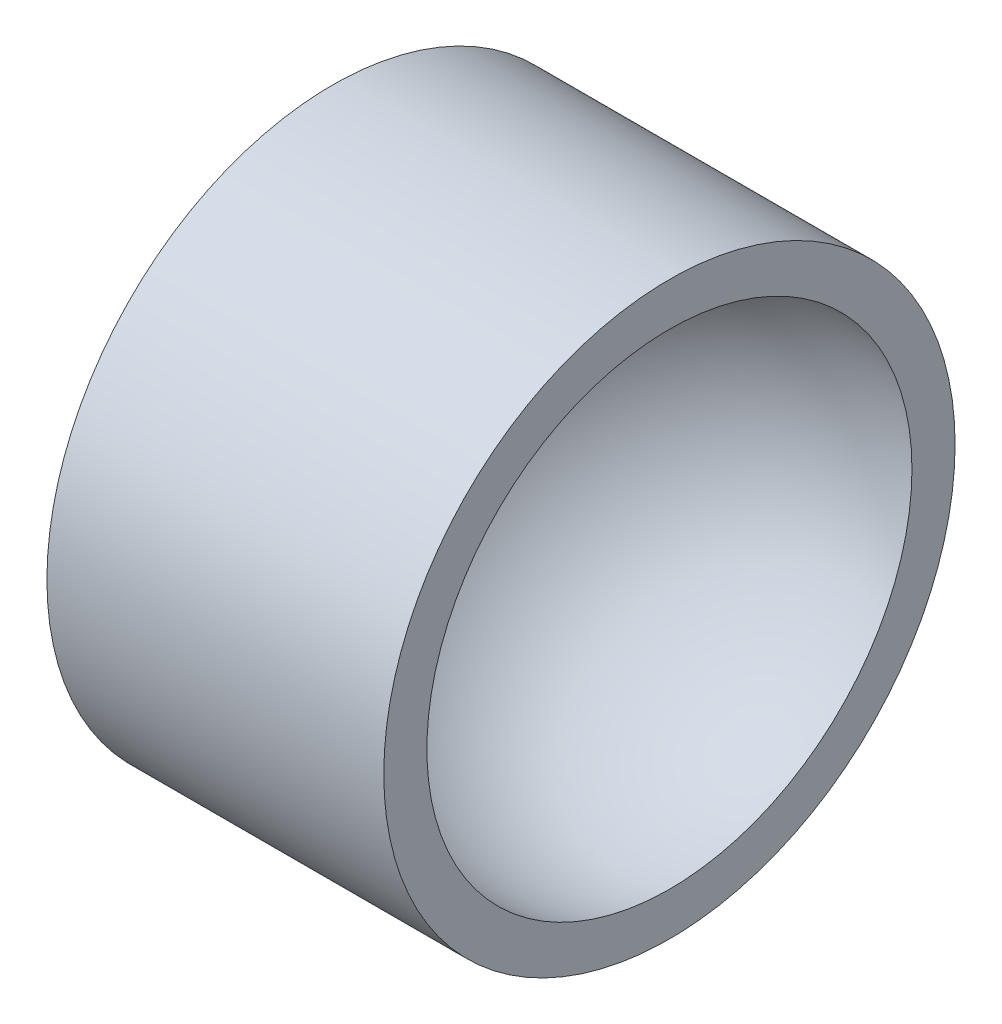
SolidWorks part; units mm, degrees
ref_plane "Alzado" through (0, 0, 0) normal (0, 0, 1) x (1, 0, 0)
ref_plane "Planta" through (0, 0, 0) normal (0, 1, 0) x (1, 0, 0)
ref_plane "Vista lateral" through (0, 0, 0) normal (1, 0, 0) x (0, 0, -1)
sketch "Croquis1" plane through (0, 0, 0) normal (0, 1, 0) x (1, 0, 0)
  line L0 (-10, 0) -> (-12.141, 0)
  line L1 (1.5747, 11.6308) -> (-12.141, 11.6308)
  line L4 (-12.141, 11.6308) -> (-12.141, 0)
  line L7 (1.5747, 9.8752) -> (1.5747, 11.6308)
  arc A0 (1.5747, 9.8752) -> (-10, 0) centre (0, 0) ccw
  dimension "D1" = 10
revolve "Revolución1" add sketch "Croquis1" angle 360 about L0
